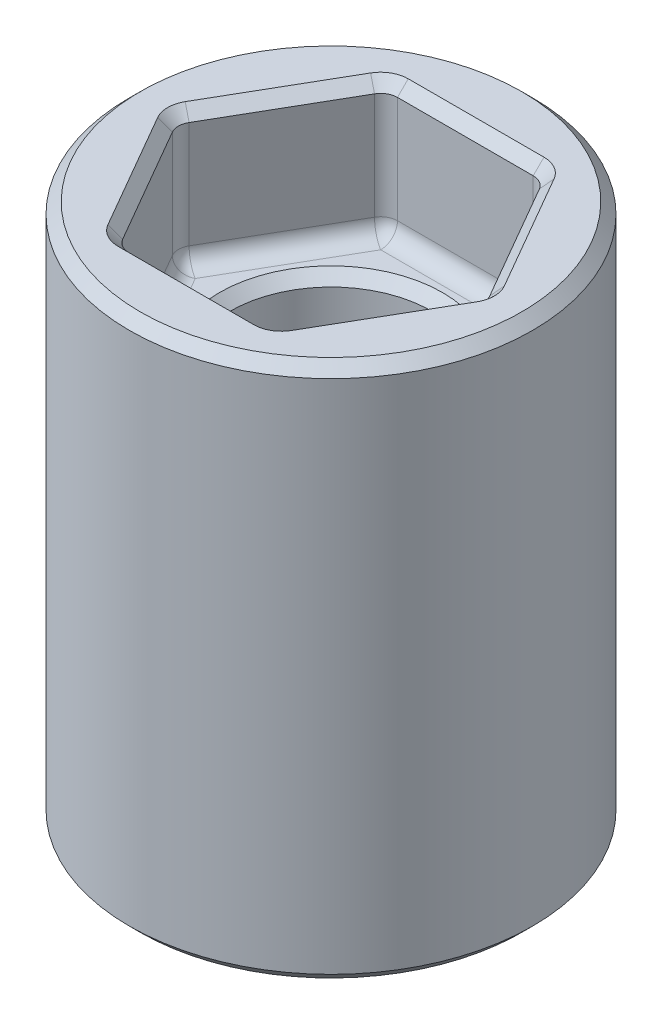
SolidWorks part; units mm, degrees
ref_plane "Front" through (0, 0, 0) normal (0, 0, 1) x (1, 0, 0)
ref_plane "Top" through (0, 0, 0) normal (0, 1, 0) x (1, 0, 0)
ref_plane "Right" through (0, 0, 0) normal (1, 0, 0) x (0, 0, -1)
sketch "Sketch4" plane through (0, 0, 0) normal (0, 1, 0) x (1, 0, 0)
  circle A0 centre (0, 0) radius 4.7625
  circle A1 centre (0, 0) radius 1.5875
  dimension "D1" = 9.525
  dimension "D2" = 3.175
extrude "Boss-Extrude1" add sketch "Sketch4" along normal blind 12.7
sketch "Sketch7" plane through (0, 0, 0) normal (0, -1, 0) x (1, 0, 0)
  line L1 (1.6241, 2.8131) -> (-1.6241, 2.8131)
  line L2 (-1.6241, 2.8131) -> (-3.2482, 0)
  line L3 (-3.2482, 0) -> (-1.6241, -2.8131)
  line L4 (-1.6241, -2.8131) -> (1.6241, -2.8131)
  line L5 (1.6241, -2.8131) -> (3.2482, 0)
  line L6 (3.2482, 0) -> (1.6241, 2.8131)
  circle A0 centre (0, 0) radius 2.8131 construction
  dimension "D1" = 5.6261
extrude "Cut-Extrude3" cut sketch "Sketch7" against normal blind 3.175
sketch "Sketch6" plane through (0, 12.7, 0) normal (0, 1, 0) x (1, 0, 0)
  line L1 (1.8331, 3.175) -> (-1.8331, 3.175)
  line L2 (-1.8331, 3.175) -> (-3.6662, 0)
  line L3 (-3.6662, 0) -> (-1.8331, -3.175)
  line L4 (-1.8331, -3.175) -> (1.8331, -3.175)
  line L5 (1.8331, -3.175) -> (3.6662, 0)
  line L6 (3.6662, 0) -> (1.8331, 3.175)
  circle A0 centre (0, 0) radius 3.175 construction
  dimension "D1" = 6.35
extrude "Cut-Extrude2" cut sketch "Sketch6" against normal blind 3.175
sketch "Sketch8" plane through (0, 9.525, 0) normal (0, 1, 0) x (1, 0, 0)
  circle A0 centre (0, 0) radius 2.3813
  dimension "D1" = 4.7625
extrude "Cut-Extrude4" cut sketch "Sketch8" against normal blind 3.175 contours A0
fillet "Fillet1" radius 0.3969 25 edges at (-2.7496, 9.525, 1.5875) (0, 9.525, 3.175) (2.7496, 9.525, -1.5875) (0, 9.525, -3.175) (-2.7496, 9.525, -1.5875) (0, 6.35, 2.3813) (3.2482, 1.5875, 0) (-1.6241, 1.5875, -2.8131) (-3.2482, 1.5875, 0) (-1.6241, 1.5875, 2.8131) (1.6241, 1.5875, 2.8131) (1.6241, 1.5875, -2.8131) (-2.4362, 3.175, -1.4065) (-2.4362, 3.175, 1.4065) (0, 3.175, 2.8131) (2.4362, 3.175, 1.4065) (2.4362, 3.175, -1.4065) (0, 3.175, -2.8131) (1.8331, 11.1125, -3.175) (-3.6662, 11.1125, 0) (-1.8331, 11.1125, 3.175) (1.8331, 11.1125, 3.175) (3.6662, 11.1125, 0) (-1.8331, 11.1125, -3.175) (2.7496, 9.525, 1.5875)
chamfer "Chamfer1" distance 0.254 angle 45 29 edges at (0, 0, 4.7625) (-1.5934, 0, 2.7599) (-2.4362, 0, 1.4065) (-3.1868, 0, 0) (-2.4362, 0, -1.4065) (-1.5934, 0, -2.7599) (0, 0, -2.8131) (1.5934, 0, -2.7599) (2.4362, 0, -1.4065) (3.1868, 0, 0) (2.4362, 0, 1.4065) (1.5934, 0, 2.7599) (0, 0, 2.8131) (0, 12.7, 4.7625) (1.8024, 12.7, -3.1218) (0, 12.7, -3.175) (-1.8024, 12.7, -3.1218) (-2.7496, 12.7, -1.5875) (-3.6048, 12.7, 0) (-2.7496, 12.7, 1.5875) (-1.8024, 12.7, 3.1218) (0, 12.7, 3.175) (1.8024, 12.7, 3.1218) (2.7496, 12.7, 1.5875) (3.6048, 12.7, 0) (2.7496, 12.7, -1.5875) (0, 6.35, 1.5875) (0, 3.175, -1.5875) (0, 9.525, 2.3813)
